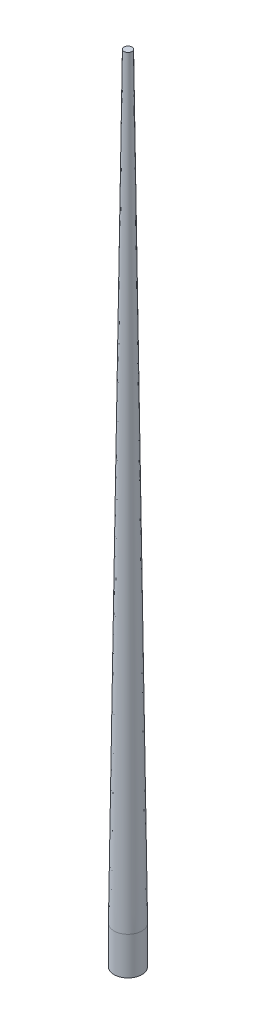
SolidWorks part; units mm, degrees
ref_plane "Front Plane" through (0, 0, 0) normal (0, 0, 1) x (1, 0, 0)
ref_plane "Top Plane" through (0, 0, 0) normal (0, 1, 0) x (1, 0, 0)
ref_plane "Right Plane" through (0, 0, 0) normal (1, 0, 0) x (0, 0, -1)
sketch "Sketch2" plane through (0, 0, 0) normal (0, 1, 0) x (1, 0, 0)
  circle A0 centre (0, 0) radius 11
  dimension "D1" = 22
extrude "Boss-Extrude1" add sketch "Sketch2" along normal blind 600 draft 0.75 and the other way blind 30
